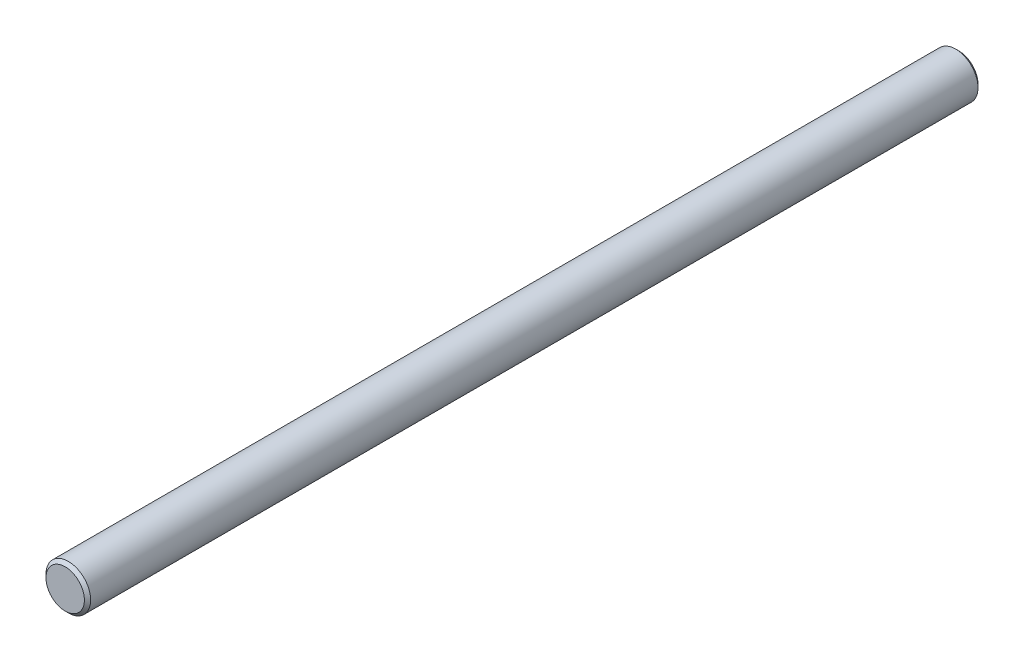
SolidWorks part; units mm, degrees
ref_plane "Front Plane" through (0, 0, 0) normal (0, 0, 1) x (1, 0, 0)
ref_plane "Top Plane" through (0, 0, 0) normal (0, 1, 0) x (1, 0, 0)
ref_plane "Right Plane" through (0, 0, 0) normal (1, 0, 0) x (0, 0, -1)
sketch "Sketch1" plane through (0, 0, 0) normal (0, 0, 1) x (1, 0, 0)
  line L0 (-15, 0) -> (15, 0) construction
  line L5 (0, 15) -> (0, -15) construction
  circle A1 centre (0, 0) radius 15
  point P7 (-15, 0)
  point P8 (15, 0)
  point P12 (0, -15)
  point P13 (0, 15)
  dimension "Diameter" = 30
sketch "Sketch2" plane through (0, 0, 0) normal (1, 0, 0) x (0, 0, -1)
  line L0 (-270, -15) -> (-270, 15) construction
  line L1 (300, -15) -> (-300, -15)
  line L2 (300, -15) -> (300, 15)
  line L3 (300, 15) -> (-300, 15)
  line L4 (-300, -15) -> (-300, 15)
  line L5 (300, -15) -> (-300, 15) construction
  line L6 (300, 15) -> (-300, -15) construction
  line L7 (270, -15) -> (270, 15) construction
  line L8 (-300, 12.9) -> (-297.9, 15) construction
  point P0 (0, 0)
  point P8 (-300, 15)
  point P9 (300, 15)
  point P14 (-270, 15)
  point P15 (-270, -15)
  point P16 (270, 15)
  point P17 (270, -15)
  point P25 (0, -15)
  dimension "Length" = 600
  dimension "D1" = 30
  dimension "D2" = 30
  dimension "Chamfer Typ," = 45
  dimension "D4" = 2.1
sketch "Sketch3" plane through (0, 0, 0) normal (0, 0, 1) x (1, 0, 0)
  circle A0 centre (0, 0) radius 15 construction
  circle A1 centre (0, 0) radius 15
extrude "Boss-Extrude1" add sketch "Sketch3" along normal up to vertex (300 mm away) and the other way up to vertex (300 mm away) up to point (0, 15, 300) other way up to point (0, 15, -300)
chamfer "Chamfer1" distance 2.1 angle 45 2 edges at (15, 0, -300) (15, 0, 300)
equation "\"D1@Sketch2\"=\"Diameter@Sketch1\""
equation "\"D2@Sketch2\"=\"Diameter@Sketch1\""
equation "\"D1@Chamfer1\"=\"Diameter@Sketch1\"*.07"
equation "\"D4@Sketch2\"=\"Diameter@Sketch1\"*.07"
equation "\"D2@Chamfer1\"=\"Chamfer Typ,@Sketch2\""
